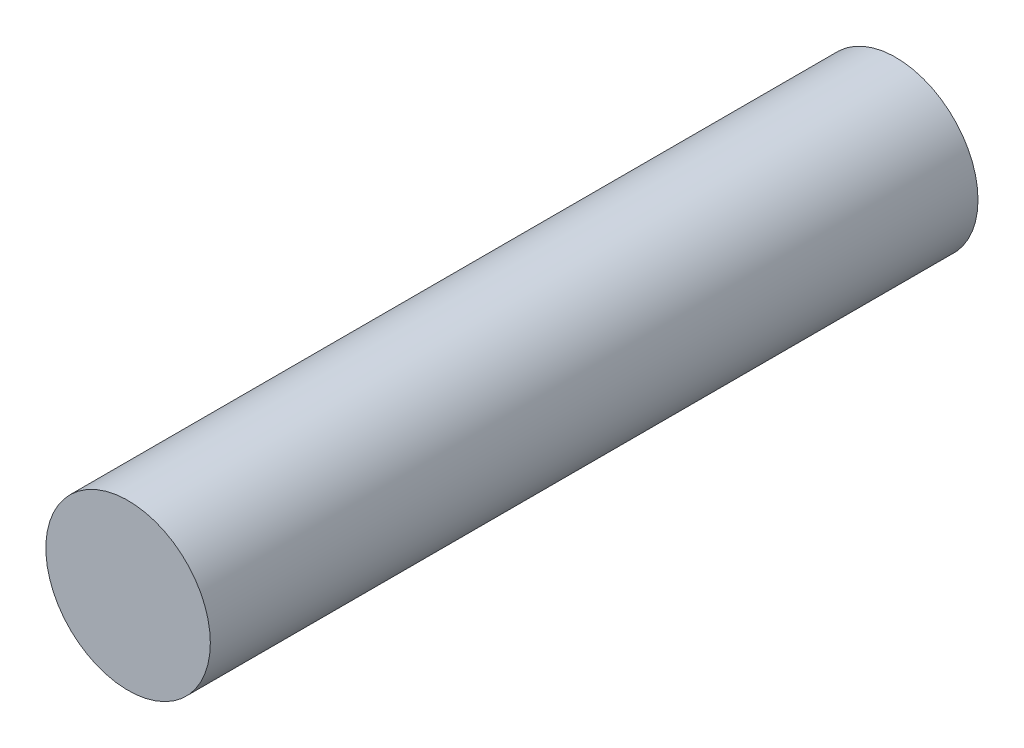
SolidWorks part; units mm, degrees
ref_plane "Front Plane" through (0, 0, 0) normal (0, 0, 1) x (1, 0, 0)
ref_plane "Top Plane" through (0, 0, 0) normal (0, 1, 0) x (1, 0, 0)
ref_plane "Right Plane" through (0, 0, 0) normal (1, 0, 0) x (0, 0, -1)
sketch "Sketch1" plane through (0, 0, 0) normal (0, 0, 1) x (1, 0, 0)
  circle A0 centre (0, 0) radius 6
  dimension "D1" = 12
extrude "Boss-Extrude1" add sketch "Sketch1" along normal mid plane 56
